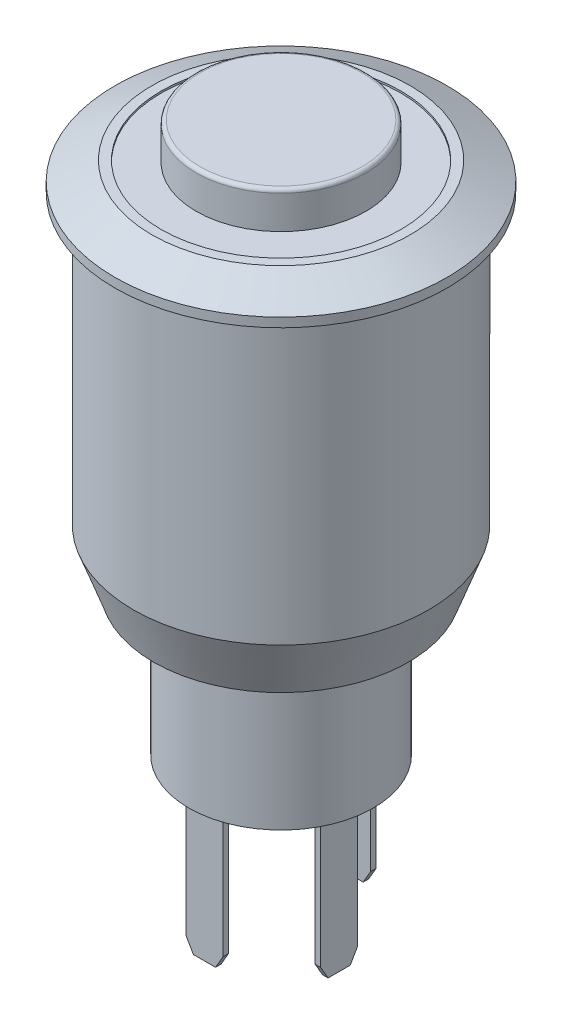
SolidWorks part; units mm, degrees
ref_plane "Front Plane" through (0, 0, 0) normal (0, 0, 1) x (1, 0, 0)
ref_plane "Top Plane" through (0, 0, 0) normal (0, 1, 0) x (1, 0, 0)
ref_plane "Right Plane" through (0, 0, 0) normal (1, 0, 0) x (0, 0, -1)
sketch "Sketch1" plane through (0, 0, 0) normal (1, 0, 0) x (0, 0, -1)
  line L1 (0, 3.4) -> (-4.6, 3.4)
  line L2 (-4.6, 3.4) -> (-4.6, 1.5)
  line L3 (-4.6, 1.5) -> (-7, 1.5)
  line L4 (-7, 1.5) -> (-9, 0.5)
  line L5 (-9, 0.5) -> (-9, 0)
  line L6 (-9, 0) -> (-8, 0)
  line L7 (-8, 0) -> (-8, -18.6)
  line L8 (-8, -18.6) -> (-5, -18.6)
  line L9 (-5, -18.6) -> (-5, -26.4)
  line L10 (-5, -26.4) -> (0, -26.4)
  line L11 (0, 14.375) -> (0, -32.104) construction
  line L12 (0, 3.4) -> (0, -26.4)
  dimension "D1" = 9.2
  dimension "D2" = 18
  dimension "D3" = 16
  dimension "D4" = 10
  dimension "D5" = 27.9
  dimension "D6" = 20.1
  dimension "D7" = 1.5
  dimension "D8" = 14
  dimension "D9" = 0.5
  dimension "D10" = 1.9
revolve "Revolve1" add sketch "Sketch1" angle 360 about L11
fillet "Fillet1" radius 0.2 1 edges at (0, 3.4, 4.6)
sketch "Sketch2" plane through (0, 1.5, 0) normal (0, 1, 0) x (1, 0, 0)
  circle A0 centre (0, 0) radius 4.6
  circle A1 centre (0, 0) radius 6.5
  circle A2 centre (0, 0) radius 4.6 construction
  dimension "D1" = 13
extrude "Cut-Extrude1" cut sketch "Sketch2" against normal blind 0.1
sketch "Sketch3" plane through (0, -26.4, 0) normal (0, -1, 0) x (1, 0, 0)
  line L0 (-1, 4) -> (1, 4)
  line L1 (-1, -4) -> (1, -4)
  line L2 (-1, 4) -> (1, -4) construction
  line L3 (-4, 1) -> (-4, -1)
  line L4 (4, 0) -> (4, 2)
  line L5 (-4, 0) -> (0, 0) construction
  point P12 (4, 1)
  dimension "D1" = 8
  dimension "D2" = 2
  dimension "D3" = 8
  dimension "D4" = 1
  dimension "D5" = 4
extrude "Extrude-Thin1" add sketch "Sketch3" along normal blind 7.6 thin thin type mid plane wall 0.3
chamfer "Chamfer1" distance 0.4 angle 60 8 edges at (1, -34, 4) (-1, -34, 4) (-4, -34, 1) (-4, -34, -1) (-1, -34, -4) (1, -34, -4) (4, -34, 0) (4, -34, 2)
chamfer "Chamfer2" distance 3 angle 20 1 edges at (0, -18.6, 8)
